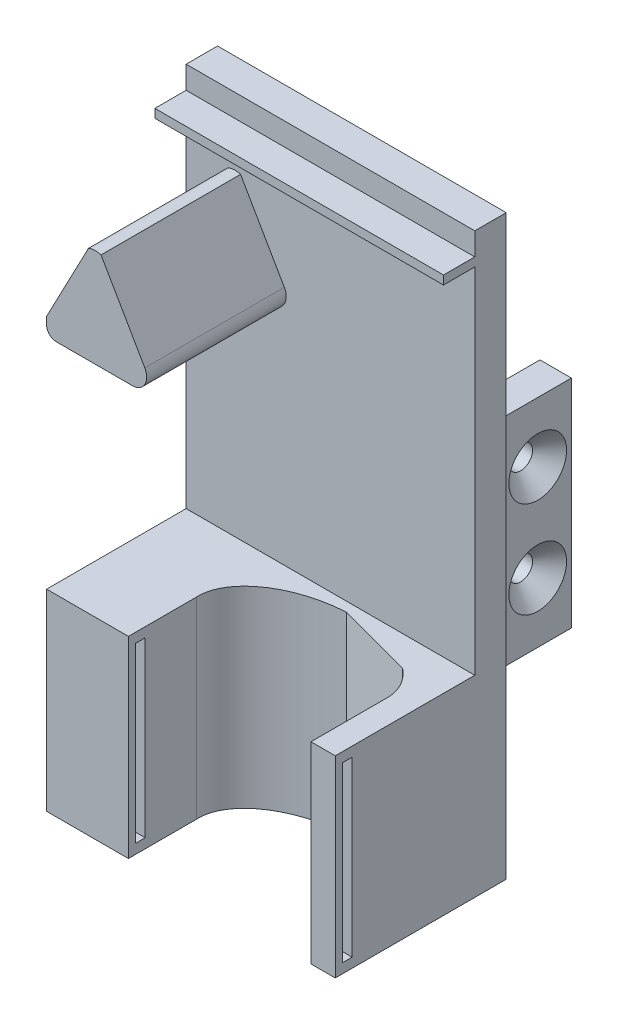
SolidWorks part; units mm, degrees
ref_plane "Front Plane" through (0, 0, 0) normal (0, 0, 1) x (1, 0, 0)
ref_plane "Top Plane" through (0, 0, 0) normal (0, 1, 0) x (1, 0, 0)
ref_plane "Right Plane" through (0, 0, 0) normal (1, 0, 0) x (0, 0, -1)
sketch "Sketch1" plane through (0, 0, 0) normal (0, 0, 1) x (1, 0, 0)
  line L1 (-30, 60) -> (30, 60)
  line L2 (-30, 60) -> (-30, -60)
  line L3 (-30, -60) -> (30, -60)
  line L4 (30, 60) -> (30, -60)
  line L5 (-30, 60) -> (30, -60) construction
  line L6 (-30, -60) -> (30, 60) construction
  point P0 (0, 0)
  dimension "D1" = 60
  dimension "D2" = 120
extrude "Boss-Extrude1" add sketch "Sketch1" along normal blind 6.54
sketch "Sketch7" plane through (0, 0, 6.54) normal (0, 0, 1) x (1, 0, 0)
  line L0 (-7, 25.5339) -> (-18.6841, 45.8173)
  line L1 (-30, 25.5339) -> (-7, 25.5339)
  line L6 (30, -60) -> (30, 60) construction
  line L15 (-21.295, 45.7034) -> (-30, 29.1154)
  line L16 (-30, 60) -> (-30, -60) construction
  line L18 (-30, 29.1154) -> (-30, 25.5339)
  line L19 (30, 60) -> (-30, 60) construction
  arc A1 (-21.295, 45.7034) -> (-18.6841, 45.8173) centre (-19.8396, 42.325) cw
  point P3 (-20, 46)
  point P9 (0, 0)
  point P10 (-18.546, 45.0415)
  point P13 (-22.3654, 44.7194)
  point P16 (-18.6841, 45.7034)
  dimension "D1" = 14
  dimension "D3" = 23
  dimension "D4" = 37
  dimension "D2" = 50
sketch "Sketch10" plane through (0, 0, 0) normal (0, 0, -1) x (-1, 0, 0)
  line L1 (20, 20) -> (26.54, 20)
  line L2 (-20, -25) -> (-20, 20)
  line L4 (-20, 20) -> (-26.54, 20)
  line L7 (20, -25) -> (20, 20)
  line L10 (-26.54, 20) -> (-26.54, -25)
  line L11 (-26.54, -25) -> (-20, -25)
  line L12 (26.54, 20) -> (26.54, -25)
  line L13 (26.54, -25) -> (20, -25)
  dimension "D1" = 6.54
  dimension "D2" = 20
  dimension "D3" = 6.54
  dimension "D4" = 20
  dimension "D5" = 45
  dimension "D6" = 45
extrude "Boss-Extrude5" add sketch "Sketch10" along normal blind 17
sketch "Sketch17" plane through (0, 0, 6.54) normal (0, 0, 1) x (1, 0, 0)
  line L0 (-30, 60) -> (-30, -60) construction
  line L1 (-30, -20) -> (30, -20)
  line L2 (-30, -20) -> (-30, -60)
  line L3 (-30, -60) -> (30, -60)
  line L4 (30, -20) -> (30, -60)
  line L5 (30, -60) -> (30, 60) construction
  line L6 (-30, -60) -> (30, -60) construction
  line L7 (30, 60) -> (-30, 60) construction
  dimension "D1" = 40
  dimension "D2" = 0
  dimension "D3" = 80
extrude "Boss-Extrude6" add sketch "Sketch17" along normal blind 29
sketch "Sketch18" plane through (0, -20, 0) normal (0, 1, 0) x (1, 0, 0)
  line L0 (5.335, -8.5264) -> (21.2913, -12.8258)
  line L1 (30, -35.54) -> (30, -6.54) construction
  line L2 (30, -35.54) -> (-30, -35.54) construction
  ellipse E0 centre (5.9723, -20.3092) end of major axis (24.9445, -19.283) minor radius 11.8 (5.335, -8.5264) -> (21.2913, -12.8258) ccw
  dimension "D1" = 43
  dimension "D2" = 5.0555
  dimension "D3" = 3.448
extrude "Cut-Extrude1" cut sketch "Sketch18" against normal up to next contours E0 L0
sketch "Sketch21" plane through (0, 0, 35.54) normal (0, 0, 1) x (1, 0, 0)
  line L0 (30, -20) -> (-30, -20) construction
  line L1 (-13, -20) -> (24.9445, -20)
  line L2 (-13, -20) -> (-13, -60)
  line L3 (-13, -60) -> (24.9445, -60)
  line L4 (24.9445, -20) -> (24.9445, -60)
  line L5 (-30, -60) -> (30, -60) construction
  line L6 (30, -60) -> (30, -20) construction
  dimension "D1" = 5.0555
  dimension "D2" = 43
extrude "Cut-Extrude2" cut sketch "Sketch21" against normal up to next contours L2 L3 L4 L1
sketch "Sketch23" plane through (-13, 0, 0) normal (1, 0, 0) x (0, 0, -1)
  line L0 (-35.54, -20) -> (-35.54, -60) construction
  line L1 (-34.04, -22) -> (-32.04, -22)
  line L2 (-34.04, -22) -> (-34.04, -58)
  line L3 (-34.04, -58) -> (-32.04, -58)
  line L4 (-32.04, -22) -> (-32.04, -58)
  line L5 (-21.3353, -60) -> (-35.54, -60) construction
  line L6 (-21.3353, -20) -> (-35.54, -20) construction
  dimension "D1" = 3.5
  dimension "D2" = 2
  dimension "D3" = 2
  dimension "D4" = 2
  dimension "D5" = 36
extrude "Cut-Extrude3" cut sketch "Sketch23" against normal blind 9
sketch "Sketch24" plane through (24.9445, 0, 0) normal (-1, 0, 0) x (0, 0, 1)
  line L0 (20.076, -60) -> (35.54, -60) construction
  line L1 (32.04, -22) -> (34.04, -22)
  line L2 (32.04, -22) -> (32.04, -58)
  line L3 (32.04, -58) -> (34.04, -58)
  line L4 (34.04, -22) -> (34.04, -58)
  line L5 (20.076, -20) -> (35.54, -20) construction
  line L6 (35.54, -20) -> (35.54, -60) construction
  dimension "D1" = 2
  dimension "D2" = 2
  dimension "D3" = 2
  dimension "D4" = 3.5
extrude "Cut-Extrude4" cut sketch "Sketch24" against normal blind 9
hole_wizard "CSK for M3 Flat Head Machine Screw4" positions "3DSketch2" profile "Sketch27" countersink size "M3" standard "ANSI Metric" end condition up to next
sketch3d "3DSketch2"
  line L4 (26.54, -25, -17) -> (26.54, -25, 0) construction
  line L5 (26.54, 20, -17) -> (26.54, -25, -17) construction
  line L6 (26.54, 20, -17) -> (26.54, 20, 0) construction
  point P14 (26.54, -12.5, -10)
  point P26 (26.54, 7.5, -10)
  dimension "D1" = 7
  dimension "D2" = 12.5
  dimension "D3" = 12.5
  dimension "D4" = 7
sketch "Sketch27" plane through (26.54, -12.5, -10) normal (0, 1, 0) x (0, 0, -1)
  line L0 (0, 0) -> (0, 6.54)
  line L1 (0, 6.54) -> (2.465, 6.54)
  line L2 (2.465, 6.54) -> (2.465, 3.535)
  line L3 (2.465, 3.535) -> (6, 0)
  line L5 (6, 0) -> (0, 0)
  line L6 (-2.465, 3.535) -> (-6, 0) construction
  line L11 (0, -6.35) -> (0, 107.95) construction
  dimension "Thru Hole Dia." = 4.93
  dimension "Thru Hole Depth" = 6.54
  dimension "Near C'Sink Dia." = 12
  dimension "Near C'Sink Angle" = 90
hole_wizard "CSK for M3 Flat Head Machine Screw5" positions "3DSketch3" profile "Sketch29" countersink size "M3" standard "ANSI Metric" end condition up to next
sketch3d "3DSketch3"
  line L0 (-26.54, -25, -17) -> (-26.54, 20, -17) construction
  line L2 (-26.54, 20, -17) -> (-26.54, 20, 0) construction
  line L3 (-26.54, -25, -17) -> (-26.54, -25, 0) construction
  point P10 (-26.54, -12.5, -10)
  point P13 (-26.54, 7.5, -10)
  dimension "D1" = 7
  dimension "D3" = 12.5
  dimension "D2" = 7
  dimension "D4" = 12.5
sketch "Sketch29" plane through (-26.54, -12.5, -10) normal (0, 1, 0) x (0, 0, 1)
  line L0 (0, 0) -> (0, 6.54)
  line L1 (0, 6.54) -> (2.465, 6.54)
  line L2 (2.465, 6.54) -> (2.465, 3.535)
  line L3 (2.465, 3.535) -> (6, 0)
  line L5 (6, 0) -> (0, 0)
  line L6 (-2.465, 3.535) -> (-6, 0) construction
  line L11 (0, -6.35) -> (0, 107.95) construction
  dimension "Thru Hole Dia." = 4.93
  dimension "Thru Hole Depth" = 6.54
  dimension "Near C'Sink Dia." = 12
  dimension "Near C'Sink Angle" = 90
extrude "Boss-Extrude8" add sketch "Sketch7" along normal blind 29
sketch "Sketch36" plane through (0, 0, 6.54) normal (0, 0, 1) x (1, 0, 0)
  line L0 (-30, 53.5) -> (30, 53.5)
  line L1 (30, 60) -> (-30, 60) construction
  line L2 (-30, 60) -> (-30, 29.1154) construction
  line L3 (-30, 55.3) -> (30, 55.3)
  line L4 (30, -20) -> (30, 60) construction
  line L5 (-30, 55.3) -> (-30, 53.5)
  line L6 (30, 55.3) -> (30, 53.5)
  dimension "D1" = 6.5
  dimension "D2" = 4.7
extrude "Boss-Extrude9" add sketch "Sketch36" along normal blind 6.5
fillet "Fillet1" radius 3 1 edges at (-7, 25.5339, 21.04)
fillet "Fillet2" radius 2 1 edges at (-30, 25.5339, 21.04)
sketch "Sketch38" plane through (0, 0, 6.54) normal (0, 0, 1) x (1, 0, 0)
  line L0 (-9.1903, 28.5339) -> (-9.1903, -36.6848) construction
  line L1 (30, -20) -> (30, 53.5) construction
  arc A0 (-12.1903, 25.5339) -> (-9.5907, 30.0314) centre (-12.1903, 28.5339) ccw construction
  arc A1 (-12.1903, 25.5339) -> (-9.5907, 30.0314) centre (-12.1903, 28.5339) ccw construction
  dimension "D1" = 39.1903
